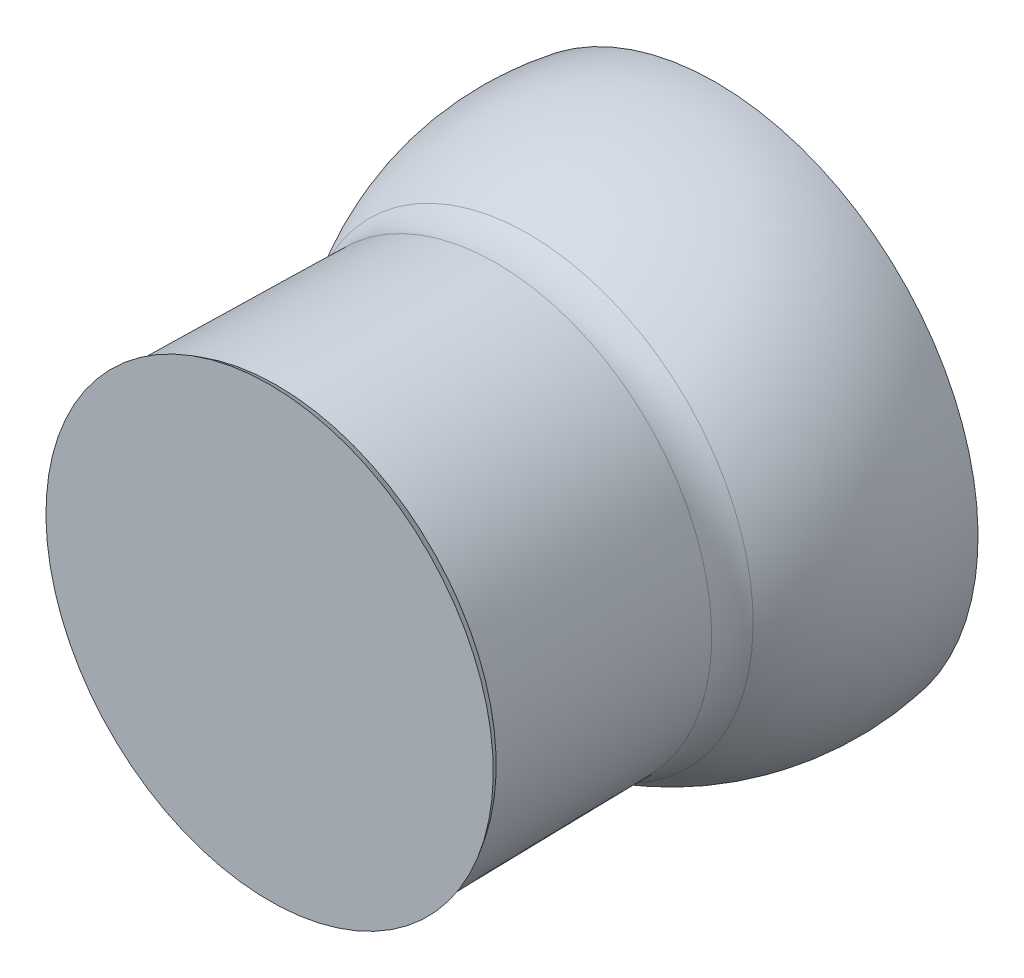
SolidWorks part; units mm, degrees
ref_plane "Front Plane" through (0, 0, 0) normal (0, 0, 1) x (1, 0, 0)
ref_plane "Top Plane" through (0, 0, 0) normal (0, 1, 0) x (1, 0, 0)
ref_plane "Right Plane" through (0, 0, 0) normal (1, 0, 0) x (0, 0, -1)
sketch "Sketch1" plane through (0, 0, 0) normal (1, 0, 0) x (0, 0, -1)
  line L0 (0, 0) -> (-50.9598, 0)
  line L2 (-50.9598, 34.2209) -> (-50.9598, 33.1794) construction
  line L6 (0, 35.8772) -> (0, 34.8622)
  line L7 (-24.752, 31.7091) -> (-24.752, 0) construction
  line L8 (0, 34.8622) -> (0, 0)
  line L9 (-50.9598, 33.1794) -> (-50.9598, 0) construction
  line L10 (-1.8421, 31.7091) -> (-37.0117, 31.7091) construction
  line L11 (-30.0543, 0) -> (-30.0543, 29.5)
  line L12 (-30.0543, 29.5) -> (-60.0543, 30)
  line L13 (22.9099, 34.8622) -> (-36.6675, 34.8622) construction
  line L14 (-24.752, 31.7091) -> (-24.752, 32.7091) construction
  line L15 (-6.1471, 0) -> (0, 34.8622) construction
  line L16 (-41.1471, 0) -> (-50.9598, 34.2209) construction
  line L17 (-60.0543, 30) -> (-61.0543, 30.5998)
  line L18 (-61.0543, 30.5998) -> (-61.0543, 0)
  line L19 (-61.0543, 0) -> (-50.9598, 0)
  line L20 (-28.9712, 33.4531) -> (-41.1471, 0) construction
  arc A0 (-28.9712, 33.4531) -> (-50.9598, 34.2209) centre (-41.1471, 0) ccw construction
  arc A1 (-19.6609, 32.7191) -> (0, 34.8622) centre (-6.1471, 0) cw construction
  arc A2 (-20.0427, 33.6433) -> (0, 35.8772) centre (-6.1471, 0) cw
  arc A3 (-28.9712, 33.4531) -> (-24.752, 32.7091) centre (-24.752, 45.0454) ccw construction
  arc A4 (-50.9598, 33.1794) -> (-29.3132, 32.5134) centre (-41.1471, 0) cw construction
  arc A5 (-29.3132, 32.5134) -> (-24.752, 31.7091) centre (-24.752, 45.0454) ccw construction
  arc A6 (-24.752, 32.7091) -> (-20.0427, 33.6433) centre (-24.752, 45.0454) ccw construction
  arc A7 (-24.752, 31.7091) -> (-19.6609, 32.7191) centre (-24.752, 45.0454) ccw construction
  arc A9 (-20.0427, 33.6433) -> (-25.6374, 30.7423) centre (-6.1471, 0) ccw
  arc A10 (-25.6374, 30.7423) -> (-30.0543, 29.5) centre (-29.9209, 37.4989) cw
  point P9 (0, 0)
  point P10 (-6.1471, 35.4)
revolve "Revolve1" add sketch "Sketch1" angle 360 about L0
equation "\"Nominal_Diameter\"= 35mm"
equation "\"D1@Sketch1\"=\"Nominal_Diameter\" + 0.6mm"
equation "\"Wall_Thickness\"= 1mm"
equation "\"D5@Sketch1\"=\"Wall_Thickness\""
equation "\"D2@Sketch1\"=\"Nominal_Diameter\" + 0.4mm"
equation "\"D3@Sketch1\"=\"Nominal_Diameter\""
